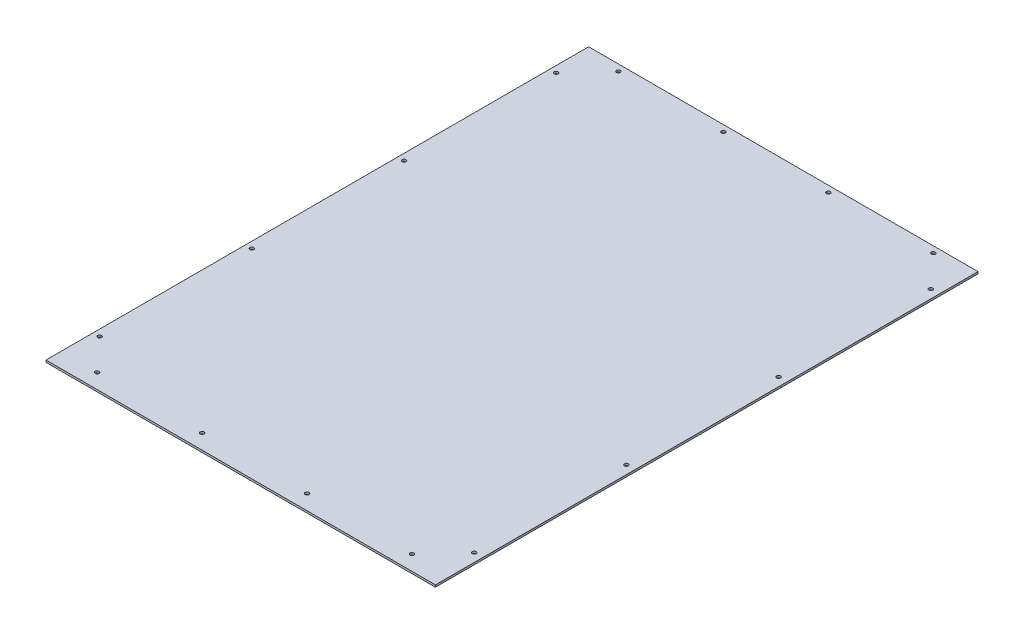
SolidWorks part; units mm, degrees
material "Acrylic (Medium-high impact)"
ref_plane "Front Plane" through (0, 0, 0) normal (0, 0, 1) x (1, 0, 0)
ref_plane "Top Plane" through (0, 0, 0) normal (0, 1, 0) x (1, 0, 0)
ref_plane "Right Plane" through (0, 0, 0) normal (1, 0, 0) x (0, 0, -1)
sketch "Sketch1" plane through (0, 0, 0) normal (0, 1, 0) x (1, 0, 0)
  line L1 (581.1266, 0) -> (0, 0)
  line L2 (581.1266, 0) -> (581.1266, 809.7266)
  line L3 (581.1266, 809.7266) -> (0, 809.7266)
  line L4 (0, 0) -> (0, 809.7266)
  line L5 (581.1266, 0) -> (0, 809.7266) construction
  line L6 (581.1266, 809.7266) -> (0, 0) construction
  line L7 (0, 809.7266) -> (0, 812.8) construction
  point P0 (0, 0)
  dimension "D1" = 581.1266
  dimension "D3" = 3.0734
  dimension "D2" = 812.8
extrude "RearSheet" add sketch "Sketch1" along normal blind 3.0734
sketch "Sketch2" plane through (0, 3.0734, 0) normal (0, 1, 0) x (1, 0, 0)
  line L0 (54.0766, 800.2016) -> (54.0766, 22.225) construction
  line L3 (54.0766, 809.7266) -> (54.0766, 790.6766) construction
  line L4 (581.1266, 809.7266) -> (0, 809.7266) construction
  line L5 (54.0766, 12.7) -> (54.0766, 31.75) construction
  line L8 (0, 809.7266) -> (-3.0734, 809.7266) construction
  line L9 (54.0766, 0) -> (54.0766, 12.7) construction
  line L10 (0, 0) -> (581.1266, 0) construction
  circle A0 centre (54.0766, 800.2016) radius 2.8956
  circle A1 centre (54.0766, 22.225) radius 2.8956
  dimension "D3" = 3.0734
  dimension "D1" = 5.7912
  dimension "D2" = 19.05
  dimension "D4" = 57.15
  dimension "D5" = 12.7
extrude "TopBottomHoles" cut sketch "Sketch2" against normal through all
sketch "Sketch3" plane through (0, 3.0734, 0) normal (0, 1, 0) x (1, 0, 0)
  line L0 (9.525, 751.84) -> (568.5282, 751.84) construction
  line L2 (9.525, 809.7266) -> (9.525, 812.8) construction
  line L3 (0, 751.84) -> (19.05, 751.84) construction
  line L5 (578.0532, 751.84) -> (559.0032, 751.84) construction
  line L12 (581.1266, 809.7266) -> (0, 809.7266) construction
  line L13 (9.525, 751.84) -> (9.525, 809.7266) construction
  line L16 (0, 809.7266) -> (0, 0) construction
  line L17 (581.1266, 0) -> (581.1266, 809.7266) construction
  circle A2 centre (9.525, 751.84) radius 2.8956
  circle A7 centre (568.5282, 751.84) radius 2.8956
  dimension "D1" = 3.0734
  dimension "D3" = 5.7912
  dimension "D8" = 5.7912
  dimension "D2" = 60.96
  dimension "D4" = 19.05
  dimension "D5" = 3.0734
extrude "VertHoles" cut sketch "Sketch3" against normal through all
pattern_linear "LPattern1" count 4 spacing 156.6333 along (1, 0, 0) of "TopBottomHoles"
pattern_linear "LPattern2" count 4 spacing 227.0845 along (0, 0, 1) of "VertHoles"
sketch "Sketch4" plane through (0, 0, 0) normal (0, -1, 0) x (1, 0, 0)
  line L0 (9.525, -67.691) -> (9.525, 0) construction
  line L1 (0, 0) -> (581.1266, 0) construction
  line L2 (54.0766, -19.3294) -> (9.525, -19.3294) construction
  line L3 (10.033, -19.3294) -> (9.017, -19.3294)
  line L4 (9.017, -19.3294) -> (9.017, -20.5994)
  line L5 (9.017, -20.5994) -> (8.509, -20.5994)
  line L6 (8.509, -20.5994) -> (9.525, -21.8694)
  line L7 (10.033, -19.3294) -> (10.033, -20.5994)
  line L8 (10.033, -20.5994) -> (10.541, -20.5994)
  line L9 (10.541, -20.5994) -> (9.525, -21.8694)
  circle A0 centre (9.525, -70.5866) radius 2.8956 construction
  circle A1 centre (54.0766, -22.225) radius 2.8956 construction
  dimension "D1" = 1.016
  dimension "D2" = 2.032
  dimension "D3" = 1.27
  dimension "D4" = 1.27
extrude "Cut-Extrude1" cut sketch "Sketch4" against normal blind 2.54
equation "\"Height\"= 32in"
equation "\"Width\"= 23in"
equation "\"Depth\"= 20in"
equation "\"Plexi\"= .121in"
equation "\"Cutwidth\"= .016in"
equation "\"Earsize\"= 1in + \"Cutwidth\" /2"
equation "\"Slotsize\" = 1in - \"CutWidth\" / 2"
equation "\"InnerWidth\" = \"Width\" - 2* \"Plexi\""
equation "\"InnerHeight\" = \"Height\" -2 * \"Plexi\""
equation "\"RearHoleSpacing\" = (\"Width\" - 2*\"RearHolesBorder\") / (\"RearNumHoles\"-1)"
equation "\"RivetDia\" = .228in"
equation "\"SlotDepth\" = \"Plexi\" + 0.75in + .005in"
equation "\"SideHoleSpacing\"= (\"InnerHeight\" - 2*\"SideHolesBorder\") / (\"SideNumHoles\"-1)"
equation "\"SideSlotWidth\"   = \"Plexi\"+.005in"
equation "\"SidePanelVertSpacing\" = (\"Height\"-2*(1.75-\"Plexi\")) / 5"
equation "\"InnerDepth\" = \"Depth\" - 2*\"Plexi\""
equation "\"BottomPanelSideHoleSpacing\" = (\"InnerDepth\"-2*(1.75-\"Plexi\")) / 4"
equation "\"D1@RearSheet\"=\"Plexi\""
equation "\"D1@Sketch1\"=\"InnerWidth\"+\"Plexi\" "
equation "\"RearNumHoles\" = 4"
equation "\"RearHolesBorder\" = 2.25"
equation "\"D1@Sketch2\"=\"RivetDia\""
equation "\"Boxsize\" = .75in"
equation "\"D2@Sketch2\"=\"Boxsize\""
equation "\"D3@Sketch2\"=\"Plexi\""
equation "\"D4@Sketch2\"=\"RearHolesBorder\""
equation "\"D3@LPattern1\"=\"RearHoleSpacing\""
equation "\"D1@LPattern1\"=\"RearNumHoles\""
equation "\"SideNumHoles\"= 5"
equation "\"SideHolesBorder\"= 1.5"
equation "\"D1@Sketch3\"=\"Plexi\""
equation "\"SideVertNumHoles\" = 4"
equation "\"SideVertHolesBorder\" = \"CornerCube\"+\"FingerLength\"+1.50"
equation "\"SideVertHoleSpacing\" = (\"SideVertBarLength\" - 2*(\"SideVertHolesBorder\"-\"Plexi\"-\"CornerCube\")) / (\"SideVertNumHoles\"-1)"
equation "\"D2@Sketch3\"=\"RearSideVertHolesBorder\""
equation "\"D4@Sketch3\"=\"Boxsize\""
equation "\"D3@LPattern2\"=\"RearSideVertHoleSpacing\""
equation "\"D1@LPattern2\"=\"RearSideVertNumHoles\""
equation "\"MagnetThickness\"= 0.125in"
equation "\"MagnetDiameter\"= 12mm"
equation "\"DoorPlexi\" = \"Plexi\""
equation "\"BasePlateThickness\" = 0.5in"
equation "\"Boxinner\" = .625in"
equation "\"CornerCube\" = 0.75in"
equation "\"FingerLength\" = 1.125in"
equation "\"RearBarLength\" = (\"InnerWidth\"-2*\"CornerCube\")"
equation "\"RearTopNumHoles\" = 4"
equation "\"RearTopHolesBorder\" = 3.1"
equation "\"RearTopHolesSpacing\" = (\"Width\" - 2*\"RearTopHolesBorder\") / (\"RearTopNumHoles\"-1)"
equation "\"SideTopNumHoles\" = 4"
equation "\"SideTopHoleOffset\"=\"CornerCube\"+\"FingerLength\"+\"Plexi\"+.5"
equation "\"SideTopHoleSpacing\" = (\"TopBarDepth\"-2*\"SideTopHoleOffset\") / (\"SideTopNumHoles\"-1)"
equation "\"SideHorizNumHoles\" = 4"
equation "\"SideHorizHoleBorder\" = 1.50"
equation "\"SideHorizHoleSpacing\" = (\"TopBarDepth\"-2*\"SideHorizHoleBorder\") / (\"SideHorizNumHoles\"-1)"
equation "\"SideVertBarLength\"=\"Height\"-\"BasePlateThickness\"-2*\"CornerCube\"-\"Plexi\""
equation "\"RearSideVertNumHoles\" = 4"
equation "\"RearSideVertHolesBorder\" = 2.4"
equation "\"RearSideVertHoleSpacing\" = (\"SideVertBarLength\" - 2*(\"RearSideVertHolesBorder\"-\"Plexi\"-\"CornerCube\")) / (\"RearSideVertNumHoles\"-1)"
equation "\"FrontDoorGap\" = .1in"
equation "\"TopDepth\" = \"Depth\"-\"DoorPlexi\"-\"FrontDoorGap\""
equation "\"TopBarDepth\" = \"Depth\"-\"DoorPlexi\"-\"Plexi\"-2*\"MagnetThickness\"-2*\"CornerCube\""
equation "\"D3@Sketch1\"=\"Plexi\""
equation "\"D2@Sketch1\"=\"Height\""
equation "\"D5@Sketch2\"=\"BasePlateThickness\""
equation "\"D5@Sketch3\"=\"Plexi\""
